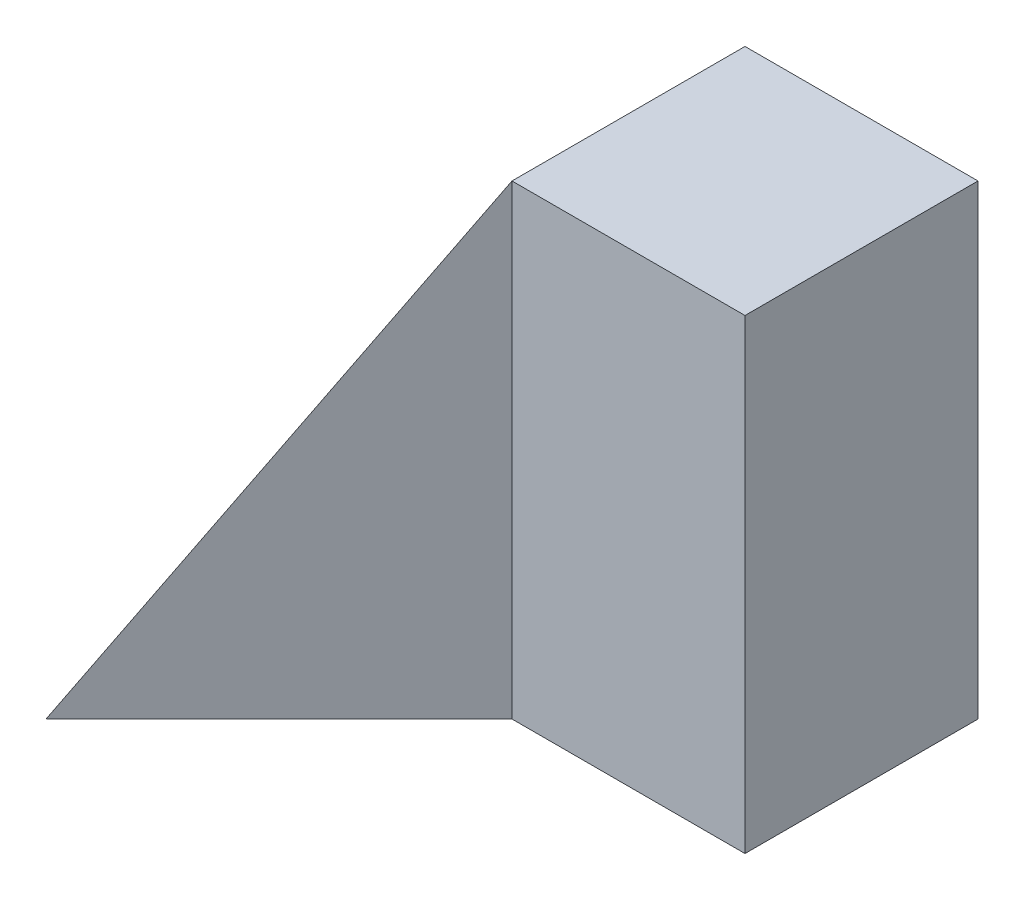
SolidWorks part; units mm, degrees
ref_plane "Front Plane" through (0, 0, 0) normal (0, 0, 1) x (1, 0, 0)
ref_plane "Top Plane" through (0, 0, 0) normal (0, 1, 0) x (1, 0, 0)
ref_plane "Right Plane" through (0, 0, 0) normal (1, 0, 0) x (0, 0, -1)
sketch "Sketch1" plane through (0, 0, 0) normal (0, 0, 1) x (1, 0, 0)
  line L1 (0, 0) -> (40, 0)
  line L2 (0, 0) -> (0, 40)
  line L3 (0, 40) -> (40, 40)
  line L4 (40, 0) -> (40, 40)
  dimension "D1" = 40
  dimension "D2" = 40
extrude "Boss-Extrude1" add sketch "Sketch1" along normal blind 40
sketch "Sketch2" plane through (0, 0, 40) normal (0, 0, 1) x (1, 0, 0)
  line L0 (0, 0) -> (20, 40)
  line L1 (40, 40) -> (0, 40) construction
  line L2 (20, 40) -> (0, 40)
  line L3 (0, 40) -> (0, 0)
extrude "Cut-Extrude1" cut sketch "Sketch2" against normal blind 40
sketch "Sketch3" plane through (0, 0, 0) normal (0, -1, 0) x (1, 0, 0)
  line L0 (40, 20) -> (20, 20)
  line L1 (40, 40) -> (40, 0) construction
  line L2 (20, 20) -> (0, 40)
  line L3 (0, 40) -> (40, 40)
  line L4 (40, 40) -> (40, 20)
  dimension "D1" = 20
extrude "Cut-Extrude2" cut sketch "Sketch3" against normal blind 40
